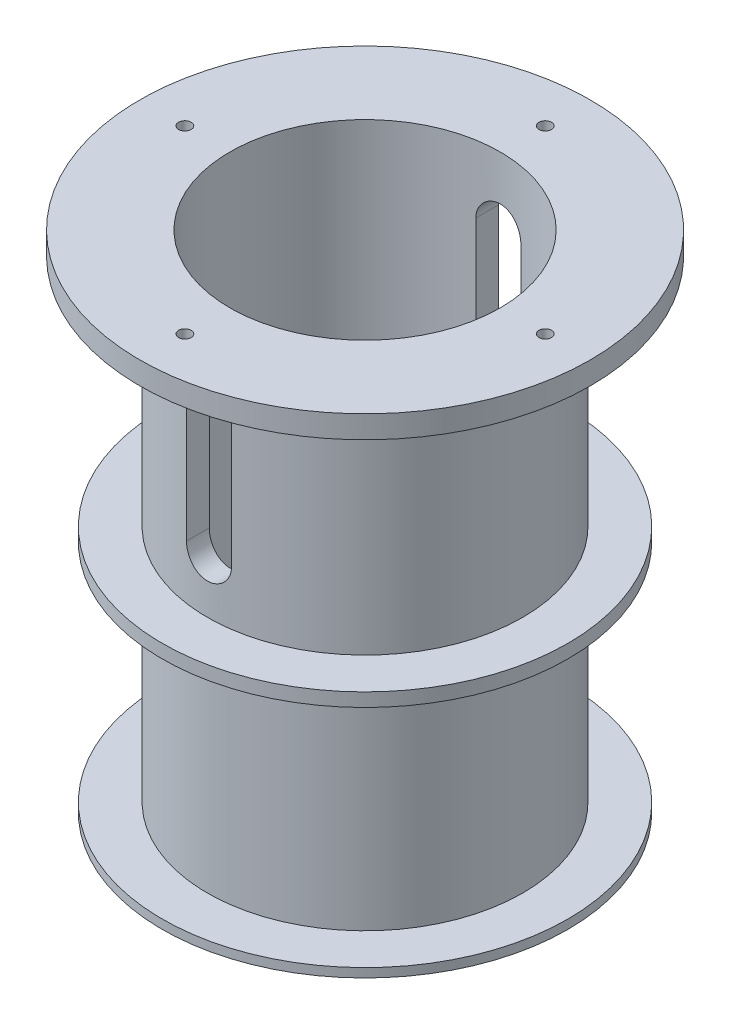
SolidWorks part; units mm, degrees
ref_plane "前视基准面" through (0, 0, 0) normal (0, 0, 1) x (1, 0, 0)
ref_plane "上视基准面" through (0, 0, 0) normal (0, 1, 0) x (1, 0, 0)
ref_plane "右视基准面" through (0, 0, 0) normal (1, 0, 0) x (0, 0, -1)
other "Configuration Table"
sketch "草图1" plane through (0, 0, 0) normal (0, 0, 1) x (1, 0, 0)
  line L0 (0, -563.1872) -> (0, 27596.1718) construction
  line L1 (-45, 0) -> (-30, 0)
  line L2 (-45, 0) -> (-45, 3)
  line L3 (-45, 3) -> (-35, 3)
  line L4 (-35, 3) -> (-35, 55)
  line L5 (-35, 55) -> (-50, 55)
  line L6 (-50, 55) -> (-50, 60)
  line L7 (-50, 60) -> (-30, 60)
  line L8 (-30, 0) -> (-30, 60)
  dimension "D1" = 57
  dimension "D2" = 60
  dimension "D3" = 90
  dimension "D4" = 3
  dimension "D5" = 70
  dimension "D6" = 5
  dimension "D7" = 100
revolve "旋转1" add sketch "草图1" angle 360 about L0
sketch "草图2" plane through (0, 0, 0) normal (0, -1, 0) x (1, 0, 0)
  circle A0 centre (0, 0) radius 30
  circle A1 centre (0, 0) radius 35
  dimension "D1" = 70
extrude "凸台-拉伸1" add sketch "草图2" along normal blind 50
sketch "草图3" plane through (0, -50, 0) normal (0, -1, 0) x (1, 0, 0)
  circle A0 centre (0, 0) radius 45
  circle A1 centre (0, 0) radius 30
extrude "凸台-拉伸2" add sketch "草图3" along normal blind 2
sketch "草图4" plane through (0, 60, 0) normal (0, 1, 0) x (1, 0, 0)
  circle A0 centre (0, 0) radius 40 construction
  circle A1 centre (0, 40) radius 1.4
  circle A2 centre (40, 0) radius 1.4
  circle A3 centre (0, -40) radius 1.4
  circle A4 centre (-40, 0) radius 1.4
  point P14 (0, 0)
  dimension "D1" = 80
  dimension "D2" = 2.8
  dimension "D3" = 4
extrude "切除-拉伸1" cut sketch "草图4" against normal up to next
sketch "草图5" plane through (0, 0, 0) normal (0, 0, 1) x (1, 0, 0)
  line L0 (0, 45) -> (0, 15) construction
  line L1 (5, 45) -> (5, 15)
  line L2 (-5, 45) -> (-5, 15)
  line L3 (-35, 0) -> (35, 0) construction
  arc A0 (5, 45) -> (-5, 45) centre (0, 45) ccw
  arc A1 (-5, 15) -> (5, 15) centre (0, 15) ccw
  point P3 (0, 30)
  dimension "D2" = 30
  dimension "D1" = 10
  dimension "D3" = 15
extrude "切除-拉伸2" cut sketch "草图5" against normal through all both and the other way through all
